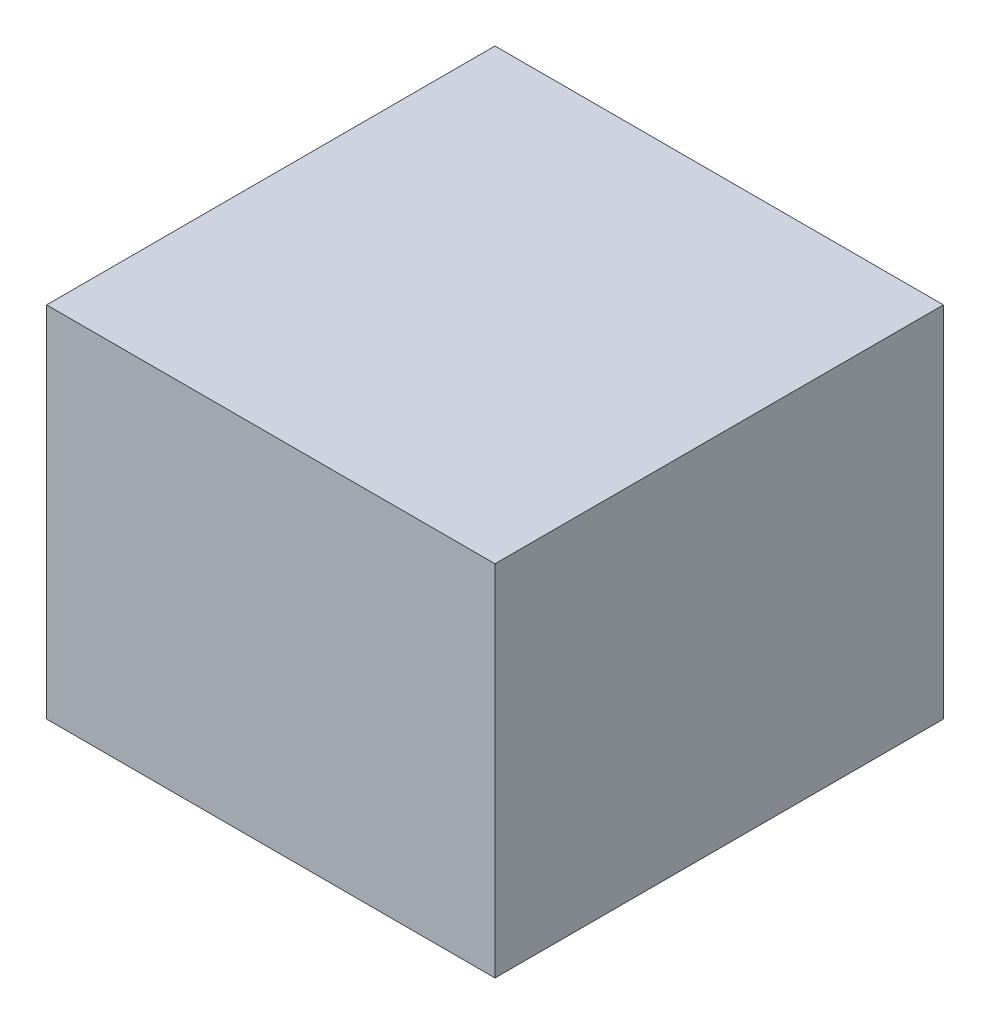
SolidWorks part; units mm, degrees
ref_plane "Front Plane" through (0, 0, 0) normal (0, 0, 1) x (1, 0, 0)
ref_plane "Top Plane" through (0, 0, 0) normal (0, 1, 0) x (1, 0, 0)
ref_plane "Right Plane" through (0, 0, 0) normal (1, 0, 0) x (0, 0, -1)
sketch "Sketch1" plane through (0, 0, 0) normal (0, 1, 0) x (1, 0, 0)
  line L1 (0, 0) -> (100, 0)
  line L2 (0, 0) -> (0, 100)
  line L3 (0, 100) -> (100, 100)
  line L4 (100, 0) -> (100, 100)
  dimension "D1" = 100
  dimension "D2" = 100
extrude "Extrude1" add sketch "Sketch1" along normal blind 80
